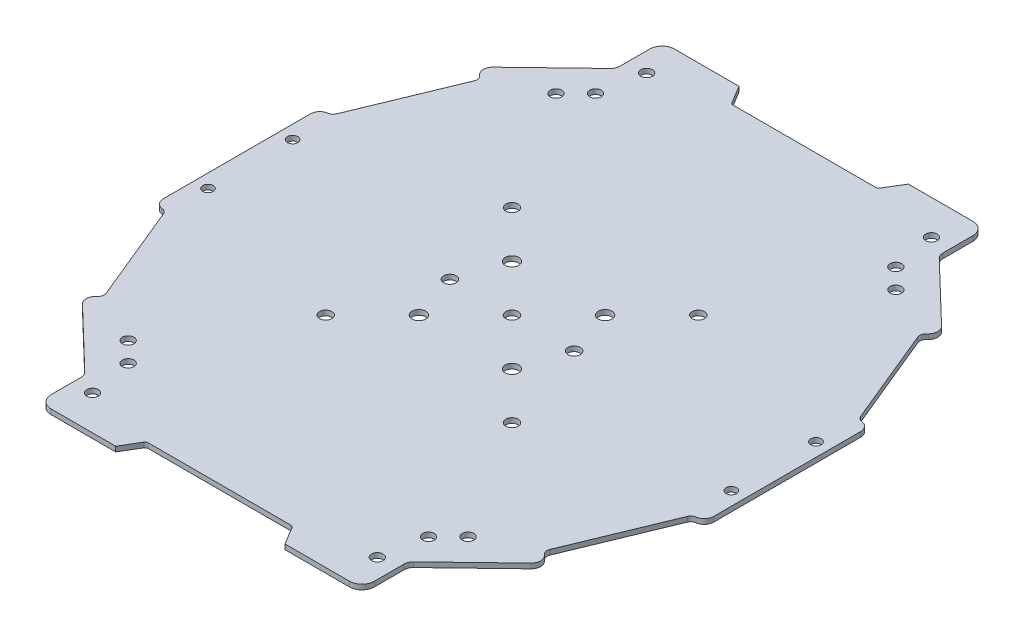
SolidWorks part; units mm, degrees
ref_plane "Front Plane" through (0, 0, 0) normal (0, 0, 1) x (1, 0, 0)
ref_plane "Top Plane" through (0, 0, 0) normal (0, 1, 0) x (1, 0, 0)
ref_plane "Right Plane" through (0, 0, 0) normal (1, 0, 0) x (0, 0, -1)
ref_plane "Plane1"
sketch "Sketch1" plane through (0, 0, 0) normal (0, 1, 0) x (-1, 0, 0)
  line L0 (74.0875, 321.0883) -> (70.3692, 327.2855)
  line L1 (70.3692, 327.2855) -> (45.5805, 327.2855)
  line L2 (45.5805, 327.2855) -> (45.5805, 312.4122)
  line L3 (45.5805, 312.4122) -> (23.246, 290.9343)
  line L4 (23.246, 290.9343) -> (26.6825, 287.3608)
  line L5 (26.6825, 287.3608) -> (12.7354, 253.539)
  line L6 (12.7354, 253.539) -> (9.0171, 253.539)
  line L7 (9.0171, 253.539) -> (9.0171, 226.8911)
  line L8 (9.0171, 226.8911) -> (9.0171, 200.2432)
  line L9 (9.0171, 200.2432) -> (12.7354, 200.2432)
  line L10 (12.7354, 200.2432) -> (26.6825, 166.4214)
  line L11 (26.6825, 166.4214) -> (23.246, 162.8479)
  line L12 (23.246, 162.8479) -> (45.5805, 141.37)
  line L13 (45.5805, 141.37) -> (45.5805, 126.4967)
  line L14 (45.5805, 126.4967) -> (70.3692, 126.4967)
  line L15 (70.3692, 126.4967) -> (74.0875, 132.6939)
  line L16 (74.0875, 132.6939) -> (97.6368, 132.6939)
  line L17 (97.6368, 132.6939) -> (121.1861, 132.6939)
  line L18 (121.1861, 132.6939) -> (124.9044, 126.4967)
  line L19 (124.9044, 126.4967) -> (149.6932, 126.4967)
  line L20 (149.6932, 126.4967) -> (149.6932, 141.37)
  line L21 (149.6932, 141.37) -> (172.0276, 162.8479)
  line L22 (172.0276, 162.8479) -> (168.5911, 166.4214)
  line L23 (168.5911, 166.4214) -> (182.5382, 200.2432)
  line L24 (182.5382, 200.2432) -> (186.2565, 200.2432)
  line L25 (186.2565, 200.2432) -> (186.2565, 226.8911)
  line L26 (186.2565, 226.8911) -> (186.2565, 253.539)
  line L27 (186.2565, 253.539) -> (182.5382, 253.539)
  line L28 (182.5382, 253.539) -> (168.5911, 287.3608)
  line L29 (168.5911, 287.3608) -> (172.0276, 290.9343)
  line L30 (172.0276, 290.9343) -> (149.6932, 312.4122)
  line L31 (149.6932, 312.4122) -> (149.6932, 327.2855)
  line L32 (149.6932, 327.2855) -> (124.9044, 327.2855)
  line L33 (124.9044, 327.2855) -> (121.1861, 321.0883)
  line L34 (121.1861, 321.0883) -> (97.6368, 321.0883)
  line L35 (97.6368, 321.0883) -> (74.0875, 321.0883)
  line L36 (97.6368, 132.6939) -> (97.6368, 321.0883) construction
  line L37 (9.0171, 226.8911) -> (186.2565, 226.8911) construction
  line L38 (67.6368, 256.8911) -> (127.6368, 196.8911) construction
  line L39 (127.6368, 256.8911) -> (67.6368, 196.8911) construction
  line L40 (42.8881, 295.782) -> (49.2662, 302.1601) construction
  line L41 (146.0075, 302.1601) -> (152.3856, 295.782) construction
  line L42 (49.2662, 151.6221) -> (42.8881, 158.0002) construction
  line L43 (146.0075, 151.6221) -> (152.3856, 158.0002) construction
  line L126 (176.3908, 226.8911) -> (176.3908, 225.1916)
  circle A0 centre (112.6368, 211.8911) radius 2.2
  circle A1 centre (49.2662, 151.6221) radius 1.8592
  circle A2 centre (112.6368, 241.8911) radius 2.2
  circle A3 centre (82.6368, 241.8911) radius 2.2
  circle A4 centre (82.6368, 211.8911) radius 2.2
  circle A5 centre (117.6368, 226.8911) radius 2
  circle A6 centre (77.6368, 226.8911) radius 2
  circle A7 centre (97.6368, 226.8911) radius 2
  circle A22 centre (51.7777, 316.1305) radius 1.8592
  circle A23 centre (49.2662, 302.1601) radius 1.8592
  circle A24 centre (13.3551, 240.5249) radius 1.6732
  circle A27 centre (143.496, 137.6517) radius 1.8592
  circle A28 centre (146.0075, 151.6221) radius 1.8592
  circle A30 centre (143.496, 316.1305) radius 1.8592
  circle A33 centre (181.9185, 240.5249) radius 1.6732
  circle A54 centre (146.0075, 302.1601) radius 1.8592
  circle A55 centre (181.9185, 213.2573) radius 1.6732
  circle A74 centre (13.3551, 213.2573) radius 1.6732
  circle A77 centre (51.7777, 137.6517) radius 1.8592
  circle A78 centre (67.6368, 196.8911) radius 1.9831
  circle A79 centre (67.6368, 256.8911) radius 1.9831
  circle A82 centre (42.8881, 158.0002) radius 1.8592
  circle A86 centre (152.3856, 295.782) radius 1.8592
  circle A87 centre (42.8881, 295.782) radius 1.8592
  circle A90 centre (127.6368, 256.8911) radius 1.9831
  circle A91 centre (152.3856, 158.0002) radius 1.8592
  circle A96 centre (127.6368, 196.8911) radius 1.9831
  dimension "D1" = 30
  dimension "D11" = 15
  dimension "D14" = 40
  dimension "D28" = 6.1972
  dimension "D2" = 30
  dimension "D3" = 30
  dimension "D4" = 30
  dimension "D5" = 15
  dimension "D6" = 15
  dimension "D7" = 30
  dimension "D8" = 30
  dimension "D9" = 30
  dimension "D10" = 30
  dimension "D12" = 30
  dimension "D13" = 15
  dimension "D15" = 20
  dimension "D16" = 9.02
  dimension "D17" = 9.02
  dimension "D18" = 9.02
  dimension "D19" = 9.02
  dimension "D20" = 10
  dimension "D21" = 10
  dimension "D22" = 10
  dimension "D23" = 10
  dimension "D24" = 45
  dimension "D25" = 45
  dimension "D26" = 45
  dimension "D27" = 45
extrude "Extrusion1" add sketch "Sketch1" along normal blind 1.6
fillet "Fillet1" radius 1 4 edges at (-121.1861, 0.8, 132.6939) (-74.0875, 0.8, 132.6939) (-74.0875, 0.8, 321.0883) (-121.1861, 0.8, 321.0883)
fillet "Fillet2" radius 4 4 edges at (-149.6932, 0.8, 126.4967) (-45.5805, 0.8, 126.4967) (-149.6932, 0.8, 327.2855) (-45.5805, 0.8, 327.2855)
fillet "Fillet3" radius 3 4 edges at (-149.6932, 0.8, 141.37) (-45.5805, 0.8, 141.37) (-45.5805, 0.8, 312.4122) (-149.6932, 0.8, 312.4122)
fillet "Fillet4" radius 3 1 edges at (-172.0276, 0.8, 290.9343)
fillet "Fillet5" radius 2 1 edges at (-168.5911, 0.8, 287.3608)
fillet "Fillet6" radius 2 1 edges at (-26.6825, 0.8, 287.3608)
fillet "Fillet7" radius 3 1 edges at (-23.246, 0.8, 290.9343)
fillet "Fillet8" radius 3 2 edges at (-172.0276, 0.8, 162.8479) (-23.246, 0.8, 162.8479)
fillet "Fillet9" radius 2 2 edges at (-26.6825, 0.8, 166.4214) (-168.5911, 0.8, 166.4214)
fillet "Fillet10" radius 2 4 edges at (-12.7354, 0.8, 200.2432) (-12.7354, 0.8, 253.539) (-182.5382, 0.8, 253.539) (-182.5382, 0.8, 200.2432)
fillet "Fillet11" radius 3 4 edges at (-186.2565, 0.8, 200.2432) (-186.2565, 0.8, 253.539) (-9.0171, 0.8, 253.539) (-9.0171, 0.8, 200.2432)
